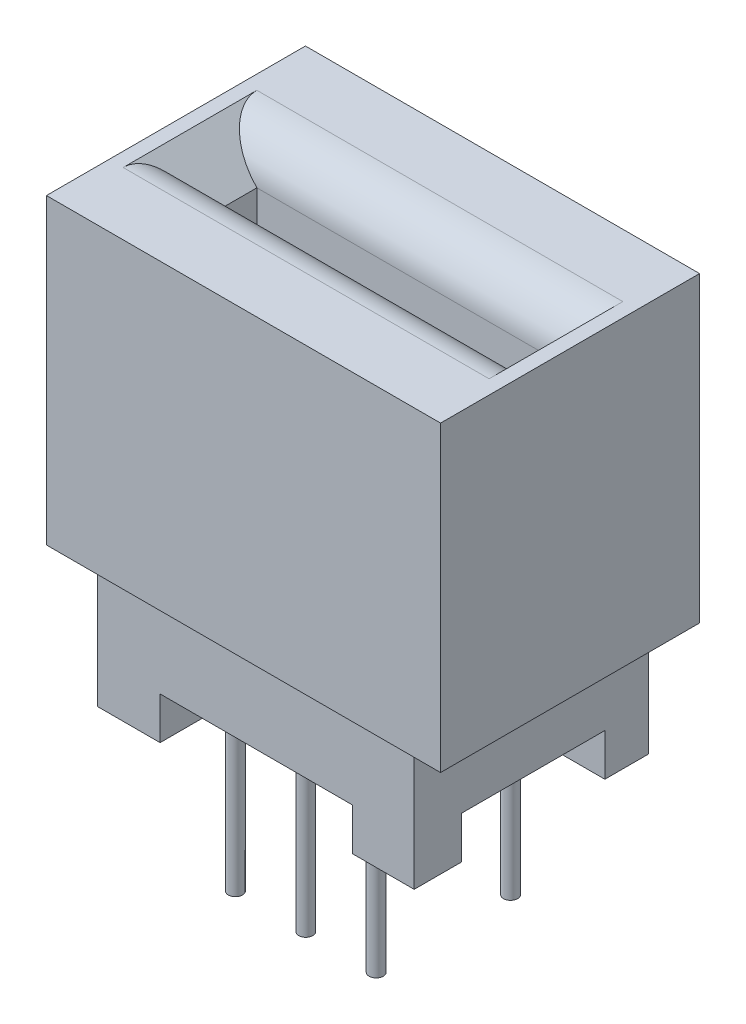
SolidWorks part; units mm, degrees
ref_plane "Front Plane" through (0, 0, 0) normal (0, 0, 1) x (1, 0, 0)
ref_plane "Top Plane" through (0, 0, 0) normal (0, 1, 0) x (1, 0, 0)
ref_plane "Right Plane" through (0, 0, 0) normal (1, 0, 0) x (0, 0, -1)
sketch "Sketch1" plane through (0, 0, 0) normal (0, 1, 0) x (1, 0, 0)
  line L0 (-7.112, -4.6736) -> (7.112, 4.6736) construction
  line L1 (-7.112, -4.6736) -> (7.112, -4.6736)
  line L2 (-7.112, -4.6736) -> (-7.112, 4.6736)
  line L3 (-7.112, 4.6736) -> (7.112, 4.6736)
  line L4 (7.112, -4.6736) -> (7.112, 4.6736)
  dimension "D1" = 9.3472
  dimension "D2" = 14.224
extrude "Boss-Extrude1" add sketch "Sketch1" against normal blind 10.922
sketch "Sketch2" plane through (0, -10.922, 0) normal (0, -1, 0) x (1, 0, 0)
  line L1 (-5.715, 4.2291) -> (5.715, 4.2291)
  line L2 (-5.715, 4.2291) -> (-5.715, -4.2291)
  line L3 (-5.715, -4.2291) -> (5.715, -4.2291)
  line L4 (5.715, 4.2291) -> (5.715, -4.2291)
  line L6 (-5.715, -4.2291) -> (5.715, 4.2291) construction
  dimension "D1" = 11.43
extrude "Boss-Extrude2" add sketch "Sketch2" along normal blind 3.048
sketch "Sketch3" plane through (0, -13.97, 0) normal (0, -1, 0) x (1, 0, 0)
  line L0 (5.715, 4.2291) -> (-5.715, 4.2291) construction
  line L1 (-5.715, 4.2291) -> (-3.4551, 4.2291)
  line L2 (-5.715, 4.2291) -> (-5.715, 2.5262)
  line L3 (-5.715, 2.5262) -> (-3.4551, 2.5262)
  line L4 (-3.4551, 4.2291) -> (-3.4551, 2.5262)
  line L5 (5.715, 4.2291) -> (3.4832, 4.2291)
  line L6 (5.715, 4.2291) -> (5.715, 2.5262)
  line L7 (5.715, 2.5262) -> (3.4832, 2.5262)
  line L8 (3.4832, 4.2291) -> (3.4832, 2.5262)
  line L10 (5.715, -4.2291) -> (3.4832, -4.2291)
  line L11 (5.715, -4.2291) -> (5.715, -2.6529)
  line L12 (5.715, -2.6529) -> (3.4832, -2.6529)
  line L13 (3.4832, -4.2291) -> (3.4832, -2.6529)
  line L14 (-5.715, -4.2291) -> (-3.4551, -4.2291)
  line L15 (-5.715, -4.2291) -> (-5.715, -2.6529)
  line L16 (-5.715, -2.6529) -> (-3.4551, -2.6529)
  line L17 (-3.4551, -4.2291) -> (-3.4551, -2.6529)
extrude "Boss-Extrude3" add sketch "Sketch3" along normal blind 1.524
sketch "Sketch4" plane through (0, -13.97, 0) normal (0, -1, 0) x (1, 0, 0)
  circle A0 centre (-2.54, -2.4257) radius 0.254
  dimension "D3" = 0.508
  dimension "D1" = 2.54
  dimension "D2" = 2.4257
extrude "Boss-Extrude4" add sketch "Sketch4" along normal blind 6.604
pattern_linear "LPattern1" count 3 spacing 2.54 along (1, 0, 0) count 2 spacing 4.8514 along (0, 0, 1) of "Boss-Extrude4"
sketch "Sketch5" plane through (0, 0, 0) normal (0, 1, 0) x (1, 0, 0)
  line L0 (-5.08, -0.889) -> (5.08, 0.889) construction
  line L1 (-5.08, 0.889) -> (5.08, 0.889)
  line L2 (-5.08, 0.889) -> (-5.08, -0.889)
  line L3 (-5.08, -0.889) -> (5.08, -0.889)
  line L4 (5.08, 0.889) -> (5.08, -0.889)
  dimension "D1" = 10.16
  dimension "D2" = 1.778
extrude "Cut-Extrude1" cut sketch "Sketch5" against normal blind 7.493
chamfer "Chamfer1" distance 1.524 angle 45 2 edges at (5.08, 0, 0) (-5.08, 0, 0)
fillet "Fillet1" radius 1.524 2 edges at (0, 0, 0.889) (0, 0, -0.889)
